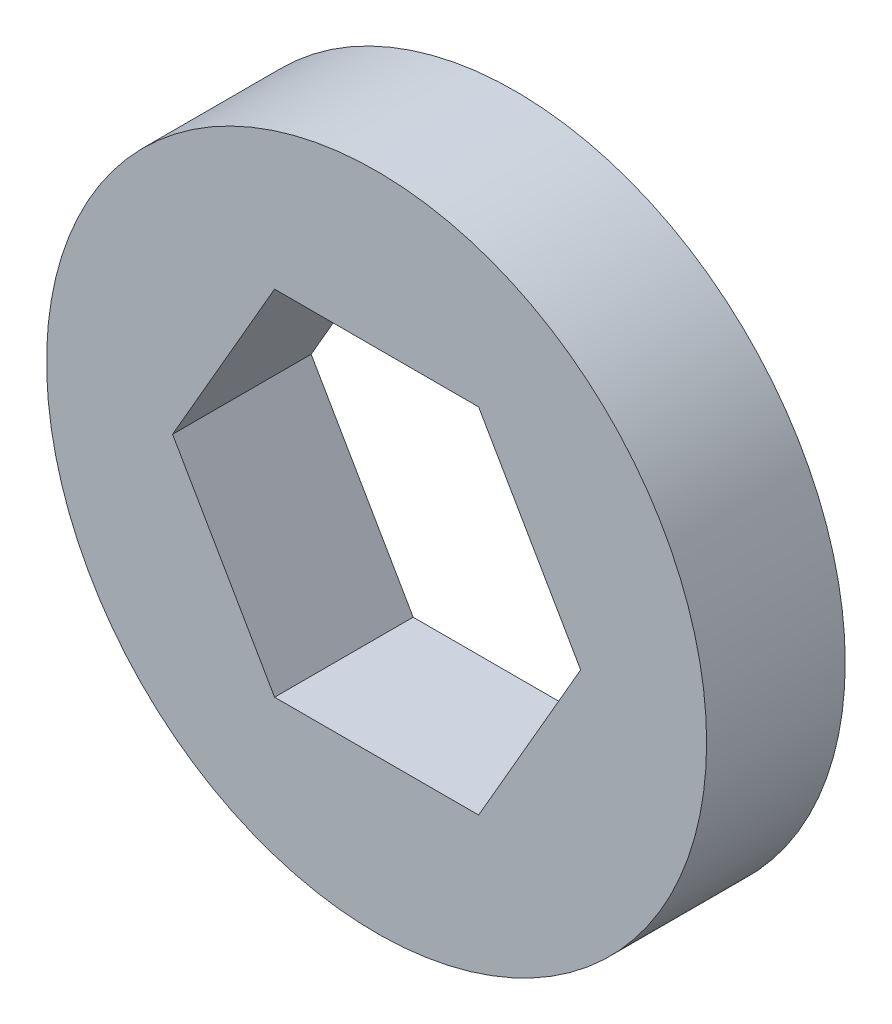
SolidWorks part; units mm, degrees
ref_plane "Front" through (0, 0, 0) normal (0, 0, 1) x (1, 0, 0)
ref_plane "Top" through (0, 0, 0) normal (0, 1, 0) x (1, 0, 0)
ref_plane "Right" through (0, 0, 0) normal (1, 0, 0) x (0, 0, -1)
sketch "Sketch1" plane through (0, 0, 0) normal (0, 0, 1) x (1, 0, 0)
  line L1 (2.9445, 0) -> (1.4722, 2.55)
  line L2 (1.4722, 2.55) -> (-1.4722, 2.55)
  line L3 (-1.4722, 2.55) -> (-2.9445, 0)
  line L4 (-2.9445, 0) -> (-1.4722, -2.55)
  line L5 (-1.4722, -2.55) -> (1.4722, -2.55)
  line L6 (1.4722, -2.55) -> (2.9445, 0)
  circle A0 centre (0, 0) radius 4.7625
  circle A1 centre (0, 0) radius 2.55 construction
  dimension "D2" = 9.525
  dimension "D1" = 5.1
extrude "Boss-Extrude1" add sketch "Sketch1" along normal blind 2
